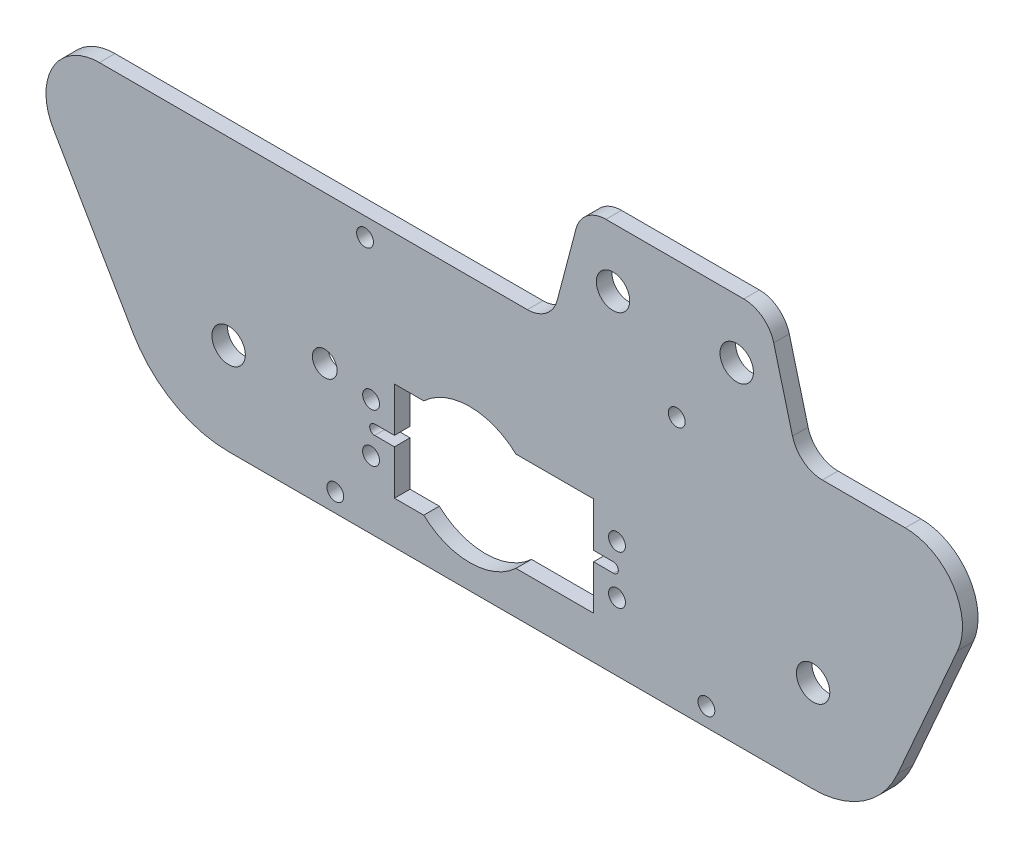
SolidWorks part; units mm, degrees
ref_plane "Front Plane" through (0, 0, 0) normal (0, 0, 1) x (1, 0, 0)
ref_plane "Top Plane" through (0, 0, 0) normal (0, 1, 0) x (1, 0, 0)
ref_plane "Right Plane" through (0, 0, 0) normal (1, 0, 0) x (0, 0, -1)
sketch "Sketch1" plane through (0, 0, 0) normal (0, 0, 1) x (1, 0, 0)
  line L8 (0, 18.9078) -> (120.015, 18.9078) construction
  line L18 (155.2575, 52.1157) -> (-50.9787, 52.1157) construction
  line L37 (0, 0) -> (120.015, 0)
  line L42 (19.7347, 25.5664) -> (0, 18.9078) construction
  line L55 (60.0075, 18.9078) -> (60.0075, 0) construction
  line L58 (138.9371, 55.9257) -> (-26.5433, 55.9257)
  line L60 (137.3256, 11.3022) -> (120.015, 0) construction
  line L61 (-19.6481, 11.3022) -> (0, 0) construction
  line L62 (149.6933, 39.4513) -> (137.3256, 11.3022)
  line L63 (-36.0198, 39.4513) -> (-19.6481, 11.3022)
  line L64 (149.6933, 39.4513) -> (-36.0198, 39.4513) construction
  line L65 (137.3256, 11.3022) -> (-19.6481, 11.3022) construction
  circle A21 centre (120.015, 18.9078) radius 3.429
  circle A22 centre (0, 18.9078) radius 3.429
  arc A25 (137.3256, 11.3022) -> (120.015, 0) centre (120.015, 18.9078) cw
  circle A27 centre (19.7347, 25.5664) radius 2.54
  arc A34 (-19.6481, 11.3022) -> (0, 0) centre (0, 22.7296) ccw
  arc A36 (138.9371, 55.9257) -> (149.6933, 39.4513) centre (138.9371, 44.1772) cw
  arc A37 (-26.5433, 55.9257) -> (-36.0198, 39.4513) centre (-26.5433, 44.9629) ccw
  dimension "D5" = 18.9078
  dimension "D8" = 59.818
  dimension "D3" = 20.6736
  dimension "D11" = 52.1157
  dimension "D2" = 6.858
  dimension "D10" = 5.08
  dimension "D4" = 18.645
  dimension "D6" = 20.8278
  dimension "D7" = 120.015
  dimension "D9" = 3.81
  dimension "D12" = 39.4513
extrude "Boss-Extrude1" add sketch "Sketch1" along normal blind 3.2004
sketch "Sketch2" plane through (0, 0, 0) normal (0, 0, -1) x (-1, 0, 0)
  line L0 (-60.0075, 52.1157) -> (-60.0075, 18.9078) construction
  line L1 (-155.2575, 52.1157) -> (50.9787, 52.1157) construction
  line L14 (0, 18.9078) -> (-120.015, 18.9078) construction
  line L15 (-60.0075, 7.62) -> (-60.0075, 0) construction
  line L28 (-92.0115, 52.1157) -> (-76.0095, 52.1157) construction
  line L29 (-76.0095, 52.1157) -> (-44.0055, 52.1157) construction
  line L30 (-44.0055, 52.1157) -> (-28.0035, 52.1157) construction
  line L31 (-98.1075, 3.81) -> (-21.9075, 3.81) construction
  line L32 (0, 0) -> (-120.015, 0) construction
  circle A0 centre (-92.0115, 52.1157) radius 1.7272
  circle A3 centre (-28.0035, 52.1157) radius 1.7272
  circle A4 centre (-98.1075, 3.81) radius 1.7272
  circle A6 centre (-21.9075, 3.81) radius 1.7272
  point P11 (-36.0045, 52.1157)
  point P16 (-84.0105, 52.1157)
  point P17 (-60.0075, 3.81)
  dimension "D3" = 3.4544
  dimension "D5" = 7.62
  dimension "D1" = 76.2
  dimension "D2" = 16.002
  dimension "D4" = 48.006
extrude "Cut-Extrude1" cut sketch "Sketch2" against normal blind 3.2004
sketch "Sketch5" plane through (0, 0, 0) normal (0, 0, -1) x (-1, 0, 0)
  line L0 (0, 18.9078) -> (-120.015, 18.9078) construction
  line L6 (-74.944, 29.0678) -> (-74.944, 8.7478)
  line L7 (-34.05, 29.0678) -> (-34.05, 8.7478)
  line L12 (-54.497, 29.0678) -> (-54.497, 8.7478) construction
  line L13 (-79.747, 13.9078) -> (-79.747, 23.9078) construction
  line L14 (-29.247, 13.9078) -> (-29.247, 23.9078) construction
  line L15 (-79.747, 18.9078) -> (-29.247, 18.9078) construction
  line L21 (-74.944, 8.7478) -> (-34.05, 8.7478)
  line L25 (-74.944, 29.0678) -> (-34.05, 29.0678)
  circle A0 centre (-79.747, 23.9078) radius 1.7272
  circle A1 centre (-29.247, 13.9078) radius 1.7272
  circle A2 centre (-29.247, 23.9078) radius 1.7272
  circle A3 centre (-79.747, 13.9078) radius 1.7272
  circle A6 centre (0, 18.9078) radius 3.429 construction
  point P8 (-44.45, 18.9078)
  point P9 (-54.497, 18.9078)
  dimension "D2" = 3.4544
  dimension "D3" = 40.894
  dimension "D5" = 10.4
  dimension "D1" = 50.5
  dimension "D4" = 20.32
  dimension "D6" = 44.45
extrude "Cut-Extrude3" cut sketch "Sketch5" against normal through all
sketch "Sketch6" plane through (0, 0, 3.2004) normal (0, 0, 1) x (1, 0, 0)
  line L3 (79.747, 18.9078) -> (29.247, 18.9078) construction
  line L4 (29.986, 19.9238) -> (34.05, 19.9238)
  line L5 (29.986, 19.9238) -> (29.986, 17.8918) construction
  line L7 (29.986, 17.8918) -> (34.05, 17.8918)
  line L8 (34.05, 19.9238) -> (34.05, 17.8918)
  line L9 (74.944, 19.9238) -> (79.008, 19.9238)
  line L10 (74.944, 19.9238) -> (74.944, 17.8918)
  line L11 (74.944, 17.8918) -> (79.008, 17.8918)
  line L12 (79.008, 19.9238) -> (79.008, 17.8918) construction
  line L13 (34.05, 8.7478) -> (34.05, 29.0678) construction
  line L14 (74.944, 29.0678) -> (74.944, 8.7478) construction
  arc A6 (79.008, 19.9238) -> (79.008, 17.8918) centre (79.008, 18.9078) cw
  arc A7 (29.986, 19.9238) -> (29.986, 17.8918) centre (29.986, 18.9078) ccw
  point P22 (34.05, 18.9078)
  point P23 (74.944, 18.9078)
  dimension "D4" = 4.064
  dimension "D5" = 2.032
extrude "Cut-Extrude4" cut sketch "Sketch6" against normal up to surface (3.2004 mm away) up to face at (78.0198, 23.9078, 0)
sketch "Sketch9" plane through (0, 0, 0) normal (0, 0, -1) x (-1, 0, 0)
  line L1 (-79.747, 18.9078) -> (-29.247, 18.9078) construction
  circle A0 centre (-49.53, 18.9078) radius 13.8852
  dimension "D1" = 27.7704
  dimension "D2" = 5.08
extrude "Cut-Extrude7" cut sketch "Sketch9" against normal up to surface (3.2004 mm away) up to face at (54.497, 18.9078, 3.2004)
sketch "Sketch10" plane through (0, 0, 3.2004) normal (0, 0, 1) x (1, 0, 0)
  line L0 (78.9305, 67.9907) -> (104.3305, 67.9907) construction
  line L1 (84.0105, 67.9907) -> (84.0105, 52.1157) construction
  line L3 (91.6305, 67.9907) -> (91.6305, 55.9257) construction
  line L4 (72.5805, 80.0557) -> (110.6805, 80.0557)
  line L5 (72.5805, 80.0557) -> (66.2305, 55.9257)
  line L6 (66.2305, 55.9257) -> (117.0305, 55.9257)
  line L7 (110.6805, 80.0557) -> (117.0305, 55.9257)
  line L8 (138.9371, 55.9257) -> (-26.5433, 55.9257) construction
  line L9 (91.6305, 80.0557) -> (91.6305, 67.9907) construction
  circle A0 centre (78.9305, 67.9907) radius 3.429
  circle A1 centre (104.3305, 67.9907) radius 3.429
  point P0 (91.6305, 67.9907)
  dimension "D1" = 6.858
  dimension "D2" = 25.4
  dimension "D3" = 15.875
  dimension "D4" = 7.62
  dimension "D5" = 50.8
  dimension "D6" = 38.1
extrude "Boss-Extrude2" add sketch "Sketch10" against normal up to surface (3.2004 mm away) up to face at (78.0198, 23.9078, 0)
fillet "Fillet1" radius 6.35 4 edges at (72.5805, 80.0557, 1.6002) (110.6805, 80.0557, 1.6002) (117.0305, 55.9257, 1.6002) (66.2305, 55.9257, 1.6002)
